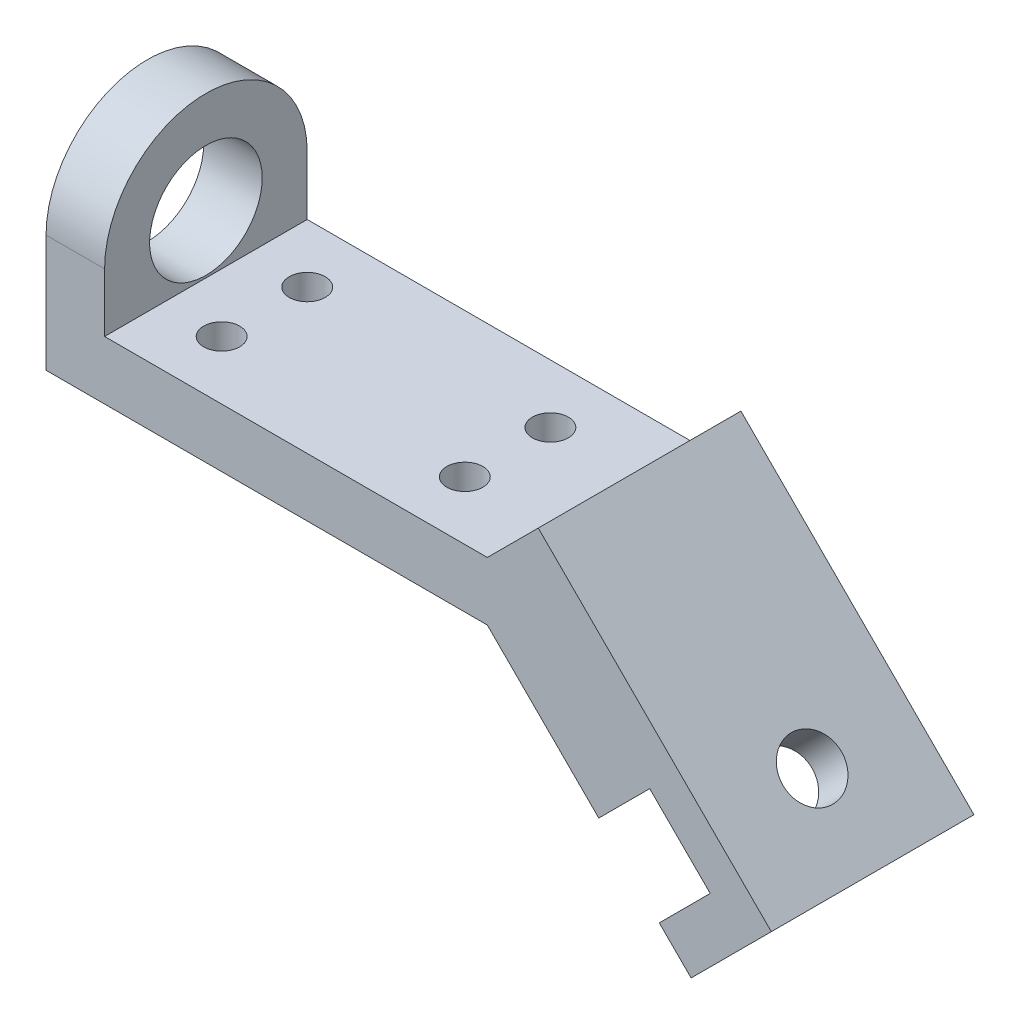
SolidWorks part; units mm, degrees
ref_plane "Piano frontale" through (0, 0, 0) normal (0, 0, 1) x (1, 0, 0)
ref_plane "Piano superiore" through (0, 0, 0) normal (0, 1, 0) x (1, 0, 0)
ref_plane "Piano destro" through (0, 0, 0) normal (1, 0, 0) x (0, 0, -1)
sketch "Schizzo1" plane through (0, 0, 0) normal (0, 0, 1) x (1, 0, 0)
  line L0 (-49, 13) -> (-49, 0)
  line L1 (55, 0) -> (-55, 0) construction
  line L2 (-49, 0) -> (49, 0)
  line L3 (49, 0) -> (94.2548, -45.2548)
  line L8 (94.2548, -45.2548) -> (100.7548, -38.7548)
  line L9 (100.7548, -38.7548) -> (49, 13)
  line L10 (49, 13) -> (-49, 13)
  line L11 (0, -55) -> (0, 55) construction
  point P0 (86.9873, -52.4428)
  point P4 (-62.4036, 21.413)
  dimension "D1" = 13
  dimension "D2" = 98
  dimension "D3" = 49
  dimension "D4" = 135
  dimension "D5" = 64
extrude "Estrusione-Estrusione1" add sketch "Schizzo1" along normal mid plane 45
sketch "Schizzo2" plane through (31, 31, 0) normal (0.7071, 0.7071, 0) x (0, 0, -1)
  line L0 (-22.5, -25.4558) -> (22.5, -25.4558)
  line L1 (22.5, -25.4558) -> (22.5, -98.6482)
  line L2 (22.5, -98.6482) -> (-22.5, -98.6482)
  line L3 (-22.5, -98.6482) -> (-22.5, -25.4558)
extrude "Estrusione-Estrusione2" add sketch "Schizzo2" along normal blind 16
sketch "Schizzo3" plane through (-49, 0, 0) normal (-1, 0, 0) x (0, 0, 1)
  line L0 (-22.5, 0) -> (-22.5, 26)
  line L1 (22.5, 0) -> (22.5, 26)
  line L2 (-22.5, 0) -> (22.5, 0)
  line L4 (22.5, 13) -> (-22.5, 13) construction
  arc A0 (22.5, 26) -> (-22.5, 26) centre (0, 26) ccw
  point P9 (22.5, 20.3132)
  dimension "D1" = 13
extrude "Estrusione-Estrusione3" add sketch "Schizzo3" against normal blind 13
sketch "Schizzo4" plane through (0, 0, 22.5) normal (0, 0, 1) x (1, 0, 0)
  line L0 (73.7487, -24.7487) -> (85.0624, -13.435)
  line L1 (49, 0) -> (94.2548, -45.2548) construction
  line L2 (85.0624, -13.435) -> (98.4975, -26.8701)
  line L3 (98.4975, -26.8701) -> (87.1838, -38.1838)
  line L4 (87.1838, -38.1838) -> (73.7487, -24.7487)
  line L5 (94.2548, -45.2548) -> (112.0685, -27.4411) construction
  dimension "D1" = 19
  dimension "D2" = 16
  dimension "D3" = 10
extrude "Taglio-Estrusione1" cut sketch "Schizzo4" against normal through all and the other way through all
sketch "Schizzo5" plane through (-36, 0, 0) normal (1, 0, 0) x (0, 0, -1)
  circle A0 centre (0, 26) radius 12.5
  dimension "D1" = 25
extrude "Taglio-Estrusione2" cut sketch "Schizzo5" against normal through all
sketch "Schizzo6" plane through (42.3137, 42.3137, 0) normal (0.7071, 0.7071, 0) x (0, 0, -1)
  line L0 (0, 51.5652) -> (0, -51.5652) construction
  line L1 (-22.5, -98.6482) -> (22.5, -98.6482) construction
  circle A0 centre (0, -79.6482) radius 6.5
  dimension "D1" = 13
  dimension "D2" = 19
extrude "Taglio-Estrusione3" cut sketch "Schizzo6" against normal through all
sketch "Schizzo7" plane through (0, 13, 0) normal (0, 1, 0) x (1, 0, 0)
  line L0 (-36, -22.5) -> (-36, 22.5) construction
  line L6 (49, 22.5) -> (-36, 22.5) construction
  circle A0 centre (-23, 9.5) radius 4
  circle A1 centre (31, 9.5) radius 4
  point P4 (0, 0)
  point P5 (0, 0)
  dimension "D1" = 8
  dimension "D4" = 13
  dimension "D2" = 13
  dimension "D3" = 54
extrude "Taglio-Estrusione4" cut sketch "Schizzo7" against normal through all
mirror "Specchia1" about plane through (0, 0, 0) normal (0, 0, 1) of "Taglio-Estrusione4"
